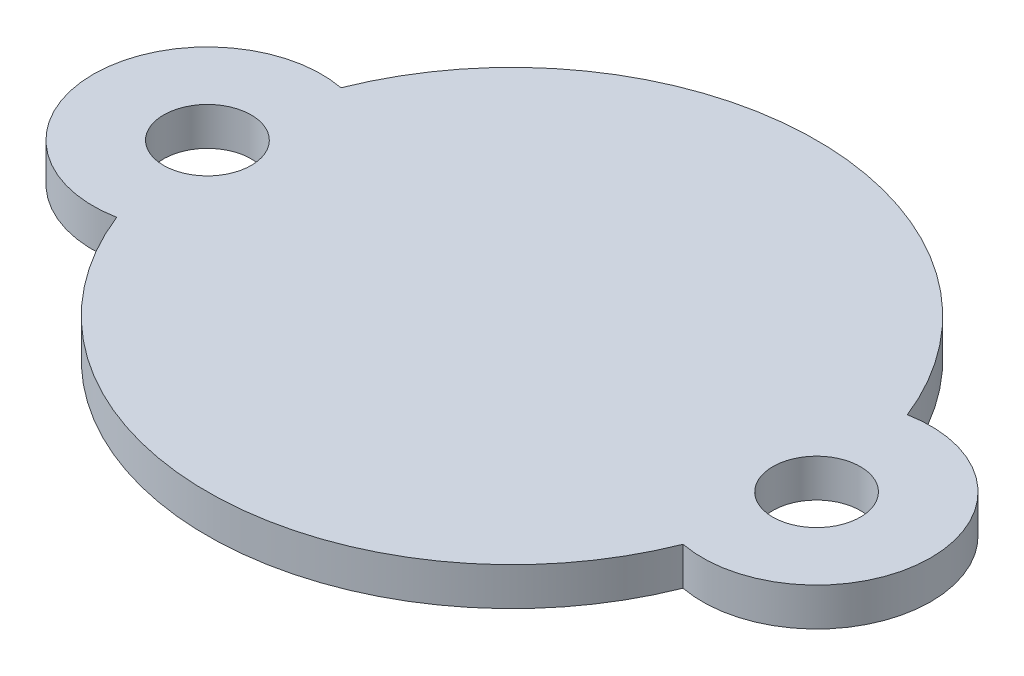
SolidWorks part; units mm, degrees
ref_plane "Front Plane" through (0, 0, 0) normal (0, 0, 1) x (1, 0, 0)
ref_plane "Top Plane" through (0, 0, 0) normal (0, 1, 0) x (1, 0, 0)
ref_plane "Right Plane" through (0, 0, 0) normal (1, 0, 0) x (0, 0, -1)
sketch "Sketch1" plane through (0, 0, 0) normal (0, 1, 0) x (1, 0, 0)
  circle A0 centre (0, 0) radius 8
  circle A2 centre (8, 0) radius 3
  circle A3 centre (-8, 0) radius 3
  circle A4 centre (8, 0) radius 1.15
  circle A5 centre (-8, 0) radius 1.15
  point P3 (8, 0)
  point P10 (-8, 0)
  dimension "D1" = 16
  dimension "D3" = 6
  dimension "D5" = 2.3
extrude "Boss-Extrude1" add sketch "Sketch1" along normal blind 1 contours A3 A0 A2 | A4 A0 A2 | A4 A0 A2 | A5 A0 A3 | A5 A0 A3
